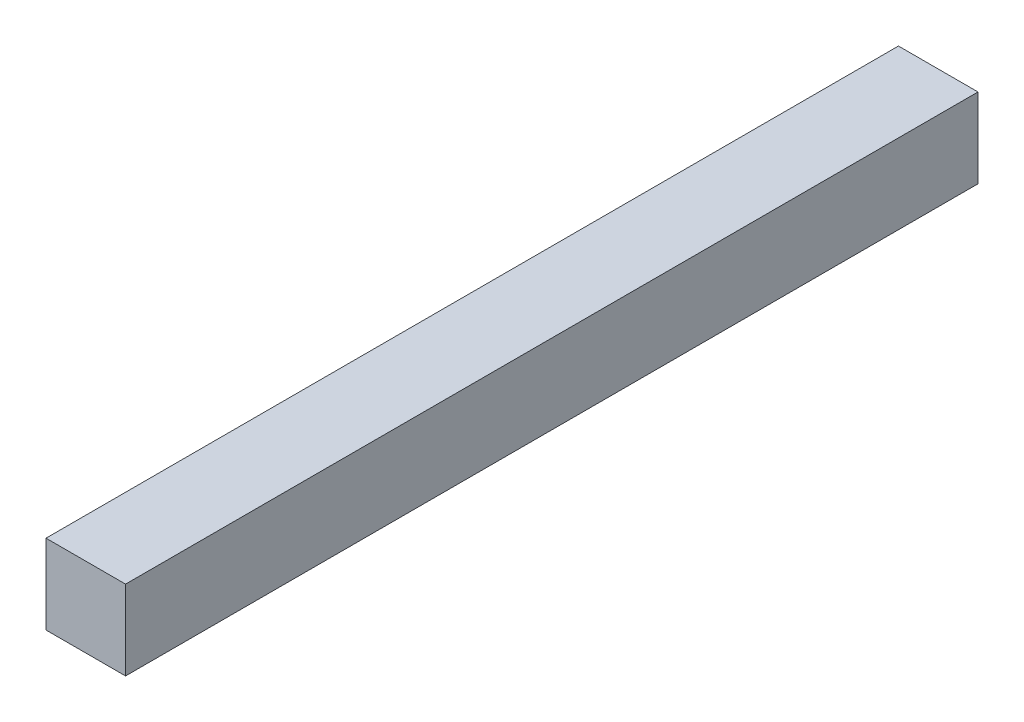
SolidWorks part; units mm, degrees
ref_plane "Front Plane" through (0, 0, 0) normal (0, 0, 1) x (1, 0, 0)
ref_plane "Top Plane" through (0, 0, 0) normal (0, 1, 0) x (1, 0, 0)
ref_plane "Right Plane" through (0, 0, 0) normal (1, 0, 0) x (0, 0, -1)
sketch "Sketch1" plane through (0, 0, 0) normal (0, 0, 1) x (1, 0, 0)
  line L1 (-1.4, 1.4) -> (1.4, 1.4)
  line L2 (-1.4, 1.4) -> (-1.4, -1.4)
  line L3 (-1.4, -1.4) -> (1.4, -1.4)
  line L4 (1.4, 1.4) -> (1.4, -1.4)
  line L5 (-1.4, 1.4) -> (1.4, -1.4) construction
  line L6 (-1.4, -1.4) -> (1.4, 1.4) construction
  point P0 (0, 0)
  dimension "D1" = 2.8
  dimension "D2" = 2.8
extrude "Boss-Extrude1" add sketch "Sketch1" along normal blind 30
